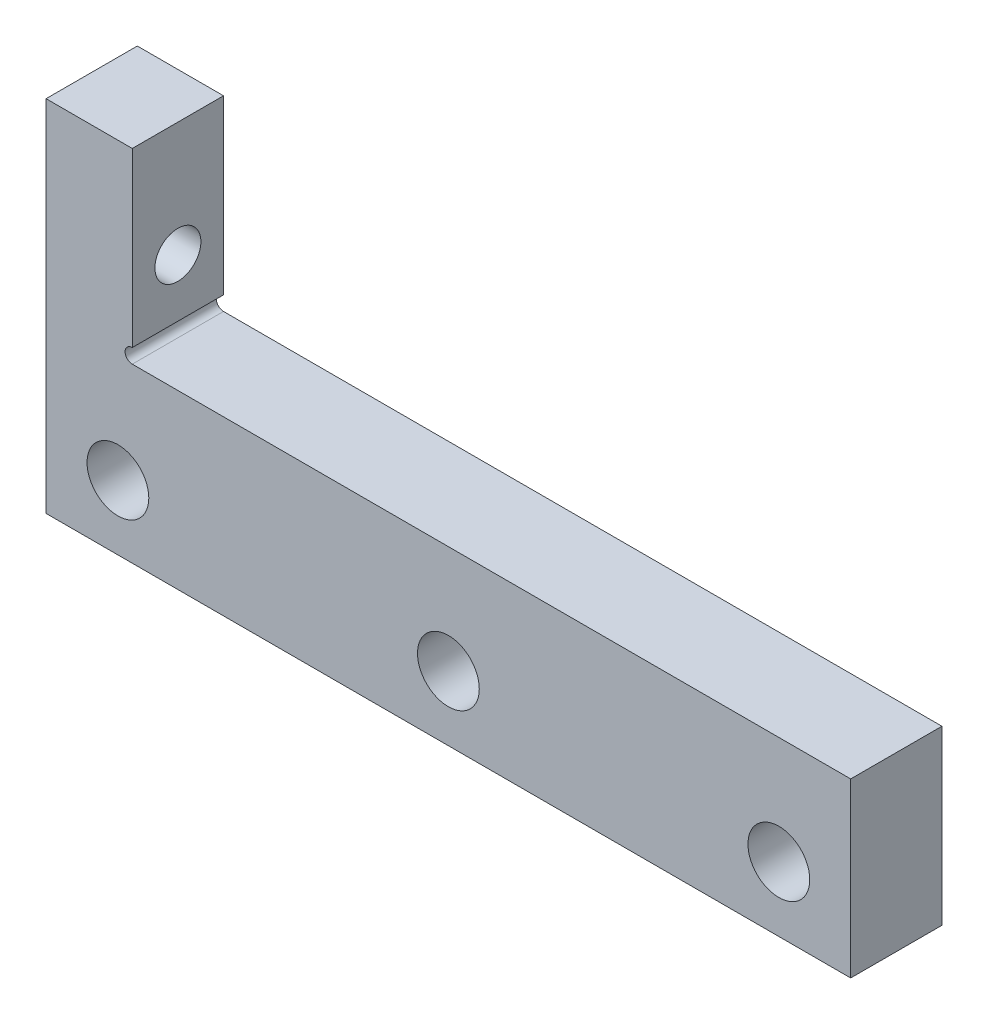
SolidWorks part; units mm, degrees
material "Plain Carbon Steel"
ref_plane "Front Plane" through (0, 0, 0) normal (0, 0, 1) x (1, 0, 0)
ref_plane "Top Plane" through (0, 0, 0) normal (0, 1, 0) x (1, 0, 0)
ref_plane "Right Plane" through (0, 0, 0) normal (1, 0, 0) x (0, 0, -1)
sketch "Sketch1" plane through (0, 0, 0) normal (0, 0, 1) x (1, 0, 0)
  line L0 (-70.5, 177.7863) -> (-64.5, 177.7863) construction
  line L1 (-70.5, 152.7863) -> (-70.5, 177.7863) construction
  line L2 (-14.5, 152.7863) -> (-70.5, 152.7863) construction
  line L3 (-14.5, 164.7863) -> (-14.5, 152.7863) construction
  line L4 (-9.5, 164.7863) -> (-59.5, 164.7863) construction
  line L5 (-59.5, 164.7863) -> (-64.5, 164.7863) construction
  line L6 (-64.5, 177.7863) -> (-64.5, 165.7863) construction
  line L7 (-52.5, 169.7863) -> (-70.5, 169.7863) construction
  line L8 (-70.5, 177.7863) -> (-64.5, 177.7863)
  line L9 (-70.5, 152.7863) -> (-70.5, 177.7863)
  line L10 (-14.5, 152.7863) -> (-70.5, 152.7863)
  line L11 (-14.5, 164.7863) -> (-14.5, 152.7863)
  line L12 (-14.5, 164.7863) -> (-59.5, 164.7863)
  line L13 (-59.5, 164.7863) -> (-64.5, 164.7863)
  line L14 (-64.5, 177.7863) -> (-64.5, 165.7863)
  line L15 (-52.5, 169.7863) -> (-70.5, 169.7863) construction
  circle A0 centre (-65.5, 157.2863) radius 2.15 construction
  circle A1 centre (-42.5, 157.2863) radius 2.15 construction
  circle A2 centre (-19.5, 157.2863) radius 2.15 construction
  circle A3 centre (-65.5, 157.2863) radius 2.15
  circle A4 centre (-42.5, 157.2863) radius 2.15
  circle A5 centre (-19.5, 157.2863) radius 2.15
  arc A6 (-64.5, 165.7863) -> (-64.5, 164.7863) centre (-64.5, 165.2863) ccw construction
  arc A7 (-64.5, 165.7863) -> (-64.5, 164.7863) centre (-64.5, 165.2863) ccw
extrude "Boss-Extrude1" add sketch "Sketch1" along normal up to surface (3.175 mm away) and the other way up to surface (3.175 mm away)
sketch "Sketch2" plane through (-70.5, 0, 0) normal (-1, 0, 0) x (0, 0, 1)
  circle A0 centre (0, 169.7863) radius 1.6
  circle A1 centre (0, 169.7863) radius 1.35 construction
  dimension "D1" = 3.2
extrude "Cut-Extrude1" cut sketch "Sketch2" against normal up to next
sketch "Sketch3" plane through (-70.5, 0, 0) normal (-1, 0, 0) x (0, 0, 1)
  circle A0 centre (0, 169.7863) radius 3
  circle A1 centre (0, 169.7863) radius 1.6 construction
  dimension "D1" = 6
extrude "Cut-Extrude2" cut sketch "Sketch3" against normal blind 2.5
sketch "Sketch4" plane through (-70.5, 0, 0) normal (-1, 0, 0) x (0, 0, 1)
  line L0 (0, 164.2863) -> (0, 175.2863) construction
  line L1 (-3.175, 152.7863) -> (-3.175, 177.7863) construction
  line L2 (3.175, 177.7863) -> (3.175, 152.7863) construction
  line L3 (0, 169.7863) -> (8.0005, 169.7863) construction
  circle A0 centre (0, 175.2863) radius 1.35
  circle A1 centre (0, 164.2863) radius 1.35
  circle A2 centre (0, 169.7863) radius 3 construction
  dimension "D1" = 2.7
  dimension "D2" = 11
extrude "Cut-Extrude3" cut sketch "Sketch4" against normal blind 5
